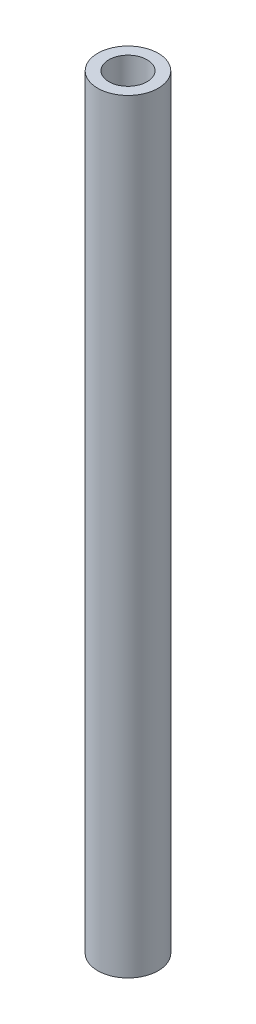
SolidWorks part; units mm, degrees
ref_plane "Alzado" through (0, 0, 0) normal (0, 0, 1) x (1, 0, 0)
ref_plane "Planta" through (0, 0, 0) normal (0, 1, 0) x (1, 0, 0)
ref_plane "Vista lateral" through (0, 0, 0) normal (1, 0, 0) x (0, 0, -1)
sketch "Croquis1" plane through (0, 0, 0) normal (0, 1, 0) x (1, 0, 0)
  circle A0 centre (0, 0) radius 1.585
  circle A1 centre (0, 0) radius 1
  dimension "D1" = 3.17
  dimension "D2" = 0.585
extrude "Saliente-Extruir1" add sketch "Croquis1" along normal blind 40
